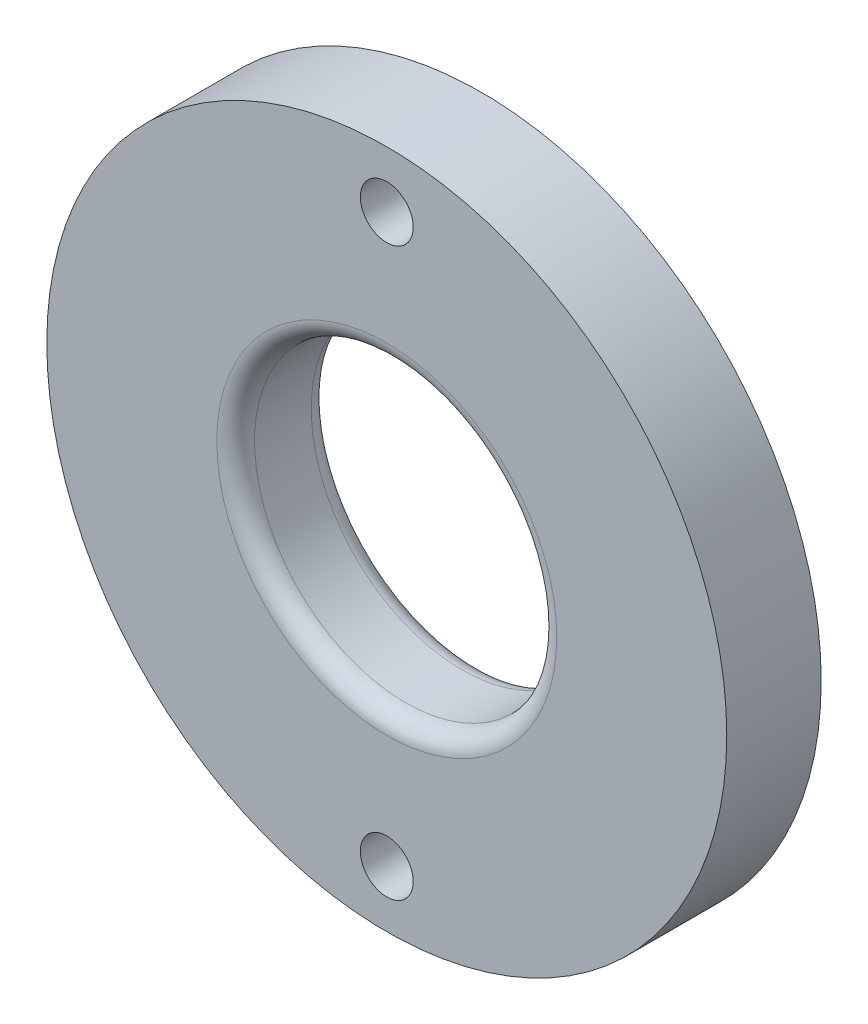
SolidWorks part; units mm, degrees
ref_plane "Front Plane" through (0, 0, 0) normal (0, 0, 1) x (1, 0, 0)
ref_plane "Top Plane" through (0, 0, 0) normal (0, 1, 0) x (1, 0, 0)
ref_plane "Right Plane" through (0, 0, 0) normal (1, 0, 0) x (0, 0, -1)
sketch "Sketch1" plane through (0, 0, 0) normal (0, 0, 1) x (1, 0, 0)
  circle A0 centre (0, 0) radius 11.43
  circle A1 centre (0, 0) radius 5.08
  dimension "D1" = 22.86
  dimension "D2" = 6.35
extrude "Boss-Extrude1" add sketch "Sketch1" along normal blind 3.175
fillet "Fillet1" radius 0.635 2 edges at (5.08, 0, 0) (5.08, 0, 3.175)
hole_wizard "#2-56 Tapped Hole1" positions "Sketch2" profile "Sketch3" tap size "#2-56" standard "ANSI Inch" end condition through all
sketch "Sketch2" plane through (0, 0, 3.175) normal (0, 0, 1) x (1, 0, 0)
  point P0 (0, 9.525)
  dimension "D1" = 9.525
sketch "Sketch3" plane through (0, 9.525, 3.175) normal (1, 0, 0) x (0, -1, 0)
  line L0 (0, 0) -> (0, 3.175)
  line L1 (0, 3.175) -> (0.889, 3.175)
  line L2 (0.889, 3.175) -> (0.889, 0)
  line L5 (0.889, 0) -> (0, 0)
  line L11 (0, -6.35) -> (0, 107.95) construction
  dimension "Thru Tap Drill Dia." = 1.778
  dimension "Thru Tap Drill Depth" = 3.175
cosmetic thread "Hole Thread1" parameters "D2"=2.1844
mirror "Mirror1" about plane through (0, 0, 0) normal (0, 1, 0) of "#2-56 Tapped Hole1"
